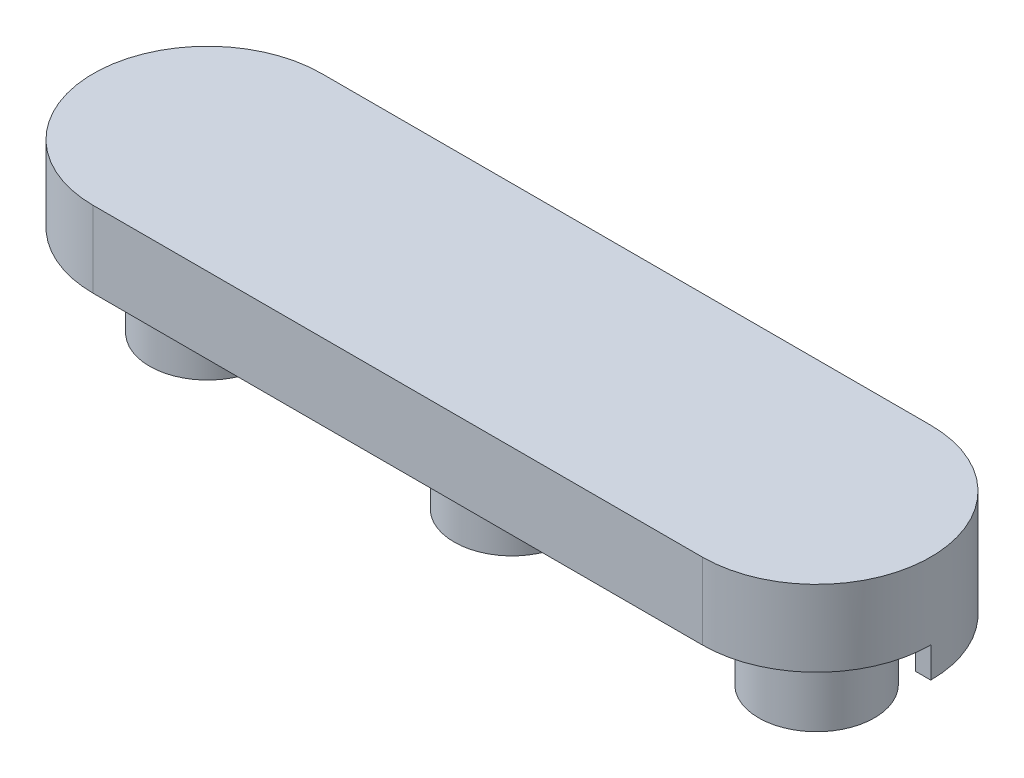
SolidWorks part; units mm, degrees
material "ABS"
ref_plane "Front Plane" through (0, 0, 0) normal (0, 0, 1) x (1, 0, 0)
ref_plane "Top Plane" through (0, 0, 0) normal (0, 1, 0) x (1, 0, 0)
ref_plane "Right Plane" through (0, 0, 0) normal (1, 0, 0) x (0, 0, -1)
sketch "Sketch1" plane through (0, 0, 0) normal (0, 1, 0) x (1, 0, 0)
  line L0 (-25.4, 0) -> (0, 0) construction
  line L1 (0, 0) -> (25.4, 0) construction
  circle A0 centre (0, 0) radius 2.0955
  circle A1 centre (25.4, 0) radius 2.0955
  circle A2 centre (-25.4, 0) radius 2.0955
  circle A3 centre (-25.4, 0) radius 3.1115
  circle A4 centre (-25.4, 0) radius 4.826
  circle A5 centre (0, 0) radius 3.1115
  circle A6 centre (0, 0) radius 4.826
  circle A7 centre (25.4, 0) radius 3.1115
  circle A8 centre (25.4, 0) radius 4.826
  dimension "D1" = 4.191
  dimension "D3" = 6.223
  dimension "D4" = 9.652
  dimension "D2" = 25.4
extrude "Plugs" add sketch "Sketch1" along normal blind 7.62 contours A2 | A4 A3 | A0 | A6 A5 | A1 | A8 A7
sketch "Sketch2" plane through (0, 7.62, 0) normal (0, 1, 0) x (1, 0, 0)
  line L0 (-25.4, 0) -> (25.4, 0) construction
  line L1 (-25.4, 9.525) -> (25.4, 9.525)
  line L2 (-25.4, -9.525) -> (25.4, -9.525)
  arc A0 (-25.4, 9.525) -> (-25.4, -9.525) centre (-25.4, 0) ccw
  arc A1 (25.4, -9.525) -> (25.4, 9.525) centre (25.4, 0) ccw
  point P4 (0, 0)
  dimension "D1" = 9.525
extrude "Back Plate" add sketch "Sketch2" along normal blind 6.35
sketch "Sketch3" plane through (0, 7.62, 0) normal (0, -1, 0) x (1, 0, 0)
  line L0 (25.4, -9.525) -> (-25.4, -9.525) construction
  line L1 (25.4, -9.525) -> (-25.4, -9.525)
  line L2 (25.4, -8.255) -> (-25.4, -8.255)
  line L3 (34.925, 0) -> (33.655, 0)
  line L4 (-33.655, 0) -> (-34.925, 0)
  arc A0 (25.4, -9.525) -> (34.925, 0) centre (25.4, 0) ccw
  arc A1 (25.4, -9.525) -> (25.4, 9.525) centre (25.4, 0) ccw construction
  arc A2 (-25.4, -9.525) -> (-34.925, 0) centre (-25.4, 0) cw
  arc A3 (-25.4, 9.525) -> (-25.4, -9.525) centre (-25.4, 0) ccw construction
  arc A5 (-25.4, -8.255) -> (-33.655, 0) centre (-25.4, 0) cw
  arc A6 (25.4, -8.255) -> (33.655, 0) centre (25.4, 0) ccw
  dimension "D2" = 1.27
extrude "Rain Guard" add sketch "Sketch3" along normal blind 2.54
